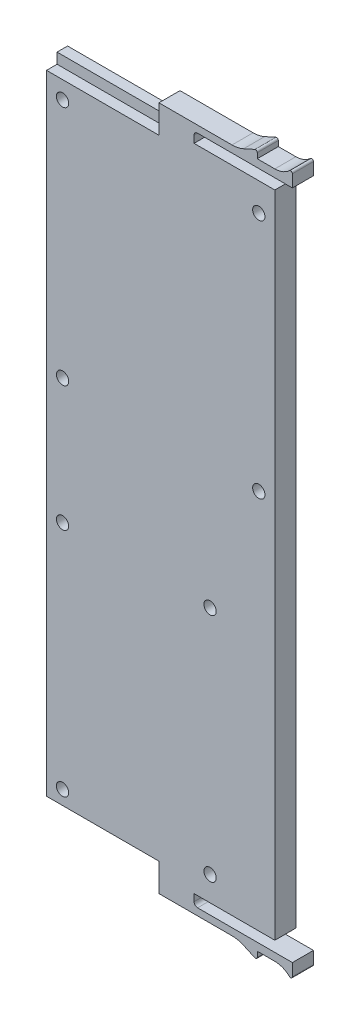
SolidWorks part; units mm, degrees
ref_plane "Front Plane" through (0, 0, 0) normal (1, 0, 0) x (0, 1, 0)
ref_plane "Top Plane" through (0, 0, 0) normal (0, 0, 1) x (0, 1, 0)
ref_plane "Right Plane" through (0, 0, 0) normal (0, 1, 0) x (-1, 0, 0)
sketch "Sketch1" plane through (0, 0, 0) normal (0, 0, 1) x (0, 1, 0)
  line L0 (-92.5, -9.5) -> (-94.5, -9.5)
  line L1 (-92.5, -32.5) -> (92.5, -32.5)
  line L2 (-92.5, -32.5) -> (-92.5, -9.5)
  line L3 (-92.5, 32.5) -> (92.5, 32.5)
  line L4 (92.5, -32.5) -> (92.5, -9.5)
  line L5 (-92.5, -32.5) -> (92.5, 32.5) construction
  line L6 (-92.5, 32.5) -> (92.5, -32.5) construction
  line L14 (-99.2, -27.5) -> (-97.7, -27.5)
  line L15 (-95.5, -10.5) -> (-95.5, -27.5)
  line L17 (-97.5, -9.5) -> (-95.5, -9.5) construction
  line L18 (-92.5, 32.5) -> (-92.5, -9.5) construction
  line L19 (0, 32.5) -> (0, -32.5) construction
  line L28 (-97.5, 0.5) -> (-92.5, 0.5)
  line L29 (-92.5, 0.5) -> (-92.5, 32.5)
  line L40 (92.5, 32.5) -> (92.5, 0.5)
  line L41 (-97.5, -9.5) -> (-97.5, 0.5)
  line L43 (-97.7, -27.5) -> (-97.7, -32.5)
  line L44 (-95.5, -27.5) -> (-95.5, -37.5)
  line L45 (-95.5, -37.5) -> (-99, -37.5)
  line L46 (-97.7, -32.5) -> (-95.5, -32.5) construction
  line L47 (-95.5, -27.5) -> (-97.7, -27.5) construction
  line L49 (92.5, -9.5) -> (94.5, -9.5)
  line L50 (97.5, 0.5) -> (92.5, 0.5)
  line L51 (95.5, -27.5) -> (97.7, -27.5) construction
  line L60 (-97.5, -9.5) -> (-97.5, -20.306)
  line L61 (-98.212, -23.6053) -> (-99.6555, -26.7938)
  line L62 (97.7, -32.5) -> (95.5, -32.5) construction
  line L63 (97.5, -9.5) -> (95.5, -9.5) construction
  line L64 (98.212, -23.6053) -> (99.6555, -26.7938)
  line L65 (97.5, -9.5) -> (97.5, -20.306)
  line L66 (95.5, -37.5) -> (99, -37.5)
  line L67 (95.5, -27.5) -> (95.5, -37.5)
  line L68 (97.7, -27.5) -> (97.7, -32.5)
  line L69 (97.5, -9.5) -> (97.5, 0.5)
  line L70 (95.5, -10.5) -> (95.5, -27.5)
  line L71 (99.2, -27.5) -> (97.7, -27.5)
  arc A0 (-99, -37.5) -> (-99.3621, -36.6552) centre (-99, -37) cw
  arc A1 (-97.7, -32.5) -> (-99.3621, -36.6552) centre (-103.725, -32.5) cw
  arc A4 (-99.6555, -26.7938) -> (-99.2, -27.5) centre (-99.2, -27) ccw
  arc A5 (-97.5, -20.306) -> (-98.212, -23.6053) centre (-105.5, -20.306) cw
  arc A6 (-94.5, -9.5) -> (-95.5, -10.5) centre (-94.5, -10.5) ccw
  arc A7 (94.5, -9.5) -> (95.5, -10.5) centre (94.5, -10.5) cw
  arc A8 (97.5, -20.306) -> (98.212, -23.6053) centre (105.5, -20.306) ccw
  arc A9 (99.6555, -26.7938) -> (99.2, -27.5) centre (99.2, -27) cw
  arc A10 (97.7, -32.5) -> (99.3621, -36.6552) centre (103.725, -32.5) ccw
  arc A11 (99, -37.5) -> (99.3621, -36.6552) centre (99, -37) ccw
  point P1 (0, 0)
  point P10 (-97.7, -28.2761)
  point P43 (-99.9752, -27.5)
  point P56 (99.9752, -27.5)
  dimension "D10" = 0.5
  dimension "D5" = 0.5
  dimension "D8" = 8
  dimension "D16" = 1
  dimension "D1" = 185
  dimension "D2" = 65
  dimension "D3" = 18
  dimension "D4" = 10
  dimension "D6" = 5
  dimension "D7" = 2
  dimension "D9" = 5
  dimension "D11" = 2.2
  dimension "D12" = 3.5
  dimension "D13" = 5
  dimension "D14" = 1.5
  dimension "D15" = 3.5
extrude "Boss-Extrude1" add sketch "Sketch1" along normal blind 6
sketch "Sketch4" plane through (-32.5, 0, 0) normal (-1, 0, 0) x (0, -1, 0)
  line L0 (0, 6) -> (0, 0) construction
  line L1 (-92.5, 6) -> (-89.5, 6)
  line L2 (-92.5, 6) -> (-92.5, 3)
  line L3 (-92.5, 3) -> (-89.5, 3)
  line L4 (-89.5, 6) -> (-89.5, 3)
  line L5 (-92.5, 6) -> (92.5, 6) construction
  line L6 (92.5, 3) -> (89.5, 3)
  line L7 (89.5, 6) -> (89.5, 3)
  line L8 (92.5, 6) -> (89.5, 6)
  line L9 (92.5, 6) -> (92.5, 3)
  dimension "D1" = 3
  dimension "D2" = 3
extrude "Cut-Extrude2" cut sketch "Sketch4" against normal up to surface (32 mm away) up to face at (-0.5, -95, 3)
sketch "Sketch5" plane through (0, 0, 6) normal (0, 0, 1) x (1, 0, 0)
  line L0 (-32.5, 84.5) -> (32.5, 84.5) construction
  line L1 (-32.5, 89.5) -> (-32.5, -89.5) construction
  line L2 (32.5, -92.5) -> (32.5, 92.5) construction
  line L3 (-32.5, 15.92) -> (32.5, 15.92) construction
  line L4 (-32.5, -19.75) -> (32.5, -19.75) construction
  line L5 (-32.5, -85.5) -> (32.5, -85.5) construction
  line L6 (0, 84.5) -> (0, 15.92) construction
  line L7 (-27.94, 84.5) -> (-27.94, 15.92) construction
  line L8 (-6.94, -19.75) -> (-6.94, -85.5) construction
  line L9 (-27.94, -19.75) -> (-27.94, -85.5) construction
  line L10 (-0.5, 89.5) -> (-32.5, 89.5) construction
  line L11 (-0.5, -89.5) -> (-32.5, -89.5) construction
  circle A0 centre (-27.94, 84.5) radius 1.75
  circle A1 centre (-27.94, 15.92) radius 1.75
  circle A2 centre (27.94, 15.92) radius 1.75
  circle A3 centre (27.94, 84.5) radius 1.75
  circle A4 centre (-27.94, -19.75) radius 1.75
  circle A5 centre (-27.94, -85.5) radius 1.75
  circle A6 centre (14.06, -85.5) radius 1.75
  circle A7 centre (14.06, -19.75) radius 1.75
  point P36 (-6.94, -19.75)
  point P37 (-6.94, -85.5)
  dimension "D8" = 3.5
  dimension "D9" = 3.5
  dimension "D10" = 3.5
  dimension "D11" = 3.5
  dimension "D1" = 68.58
  dimension "D2" = 27.94
  dimension "D3" = 5
  dimension "D4" = 65.75
  dimension "D5" = 4
  dimension "D6" = 35.67
  dimension "D7" = 21
extrude "Cut-Extrude3" cut sketch "Sketch5" against normal blind 10
